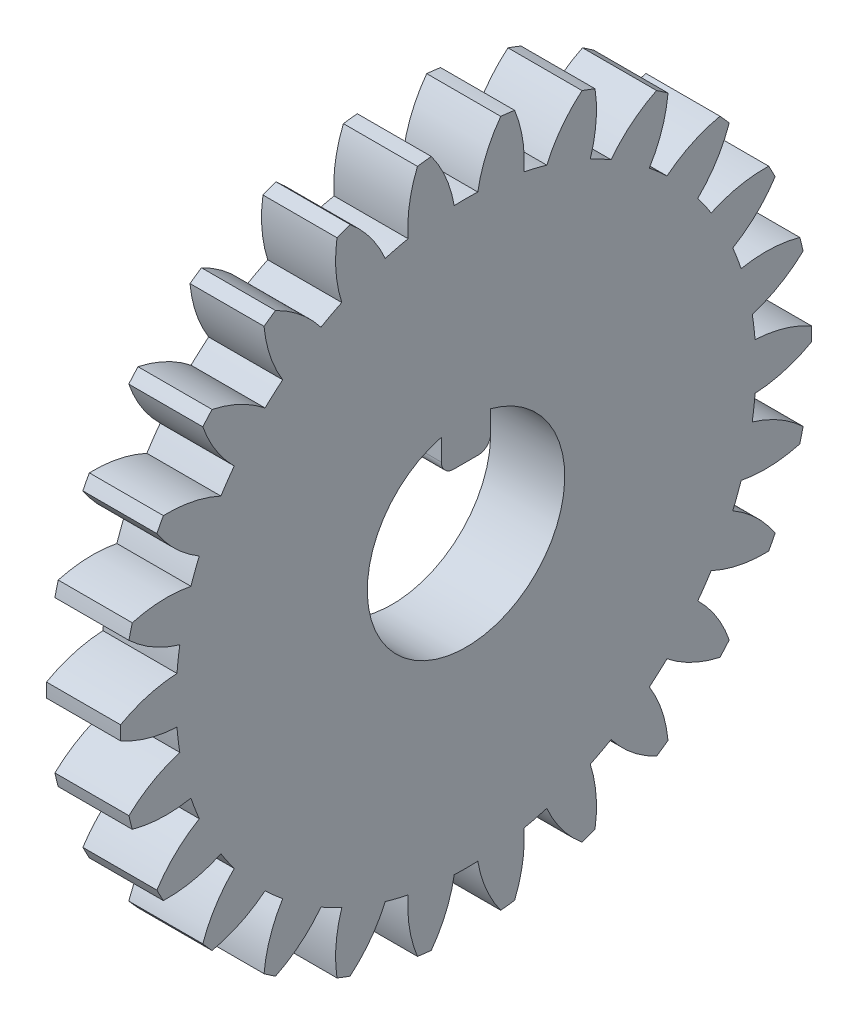
SolidWorks part; units mm, degrees
ref_plane "Plane1" through (0, 0, 0) normal (0, 0, 1) x (1, 0, 0)
ref_plane "Plane2" through (0, 0, 0) normal (0, 1, 0) x (1, 0, 0)
ref_plane "Plane3" through (0, 0, 0) normal (1, 0, 0) x (0, 0, -1)
sketch "HoldingSke" plane through (0, 0, 0) normal (0, 1, 0) x (1, 0, 0)
  line L0 (0, 0) -> (0.8988, -0.4384)
  line L1 (-15, 0) -> (100, 0) construction
  line L2 (0, 0) -> (-2.1039, 2.3779)
  line L3 (0, 0) -> (-11.863, 4.5341)
  line L4 (0, 0) -> (7.762, 3.7858)
  line L5 (0, 0) -> (-46.8476, -17.4728)
  line L6 (0, 0) -> (-2.4869, -1.6779)
  line L7 (-2.1039, 2.3779) -> (8.6586, 51.2059)
  line L8 (-76.2, 54.61) -> (-74.8, 54.61)
  line L9 (-71.009, 38.7566) -> (-53.1078, 45.2721)
  line L10 (-76.2, 71.12) -> (104.1128, 71.12)
  line L11 (0, 0) -> (-3, 0)
  line L12 (-76.2, 101.6) -> (-76.162, 101.6)
  line L13 (24.9733, 27.94) -> (52.9518, 28.4284)
  line L14 (24.9733, 27.94) -> (24.9743, 27.94)
  line L15 (24.9733, 27.94) -> (100.4006, 29.5858)
  line L16 (-63.627, -1) -> (-12.827, -1)
  circle A0 centre (0, 0) radius 4
  circle A1 centre (0, 0) radius 11.749
  circle A2 centre (0, 0) radius 37.5
  circle A3 centre (0, 0) radius 4
  dimension "MHD" = 23.498
  dimension "Hub_dia" = 75
  dimension "Bore" = 8
  dimension "MBD" = 8
  dimension "Num_teeth" = 26
  dimension "Pitch" = 1
  dimension "Overall_len" = 50
  dimension "Show_teeth" = 26
  dimension "Thickness" = 3
  dimension "OAL" = 50.0001
  dimension "T_dim" = 1.4
  dimension "Ap" = 20
  dimension "H" = 19.05
  dimension "Pitch_radius" = 180.3128
  dimension "Width" = 3
  dimension "Backlash" = 0.038
  dimension "Addendum_fac" = 1
  dimension "Dedendum_fac" = 1.25
  dimension "Clearance_fac" = 0.25
  dimension "Dedendum_add" = 0.001
  dimension "Module" = 1
sketch "BasProSke" plane through (0, 0, 0) normal (0, 1, 0) x (1, 0, 0)
  line L0 (-10, 0) -> (60, 0) construction
  line L1 (0, 0) -> (0, 14)
  line L2 (0, 0) -> (3, 0)
  line L3 (3, 0) -> (3, 14)
  line L4 (3, 14) -> (0, 14)
  dimension "Thickness" = 3
  dimension "Diameter" = 28
revolve "Base-Revolve" add sketch "BasProSke" angle 360 about L0
sketch "TooCutSke" plane through (0, 0, 0) normal (1, 0, 0) x (0, 0, -1)
  line L1 (0, 0) -> (0, 107) construction
  line L2 (0, 0) -> (-0.8514, 12.9721) construction
  line L3 (0, 0) -> (-3.1292, 25.771) construction
  line L4 (-0.8514, 12.9721) -> (-1.5646, 12.8855) construction
  arc A0 (0.477, 11.7393) -> (-0.477, 11.7393) centre (0, 0) ccw
  arc A1 (1.4241, 13.9529) -> (-1.4241, 13.9529) centre (0, 0) ccw
  circle A2 centre (0, 0) radius 13 construction
  circle A3 centre (0, 0) radius 12.216 construction
  arc A4 (-0.477, 11.7393) -> (-1.4241, 13.9529) centre (-5.6014, 10.8561) ccw
  arc A5 (1.4241, 13.9529) -> (0.477, 11.7393) centre (5.6014, 10.8561) ccw
  dimension "Root_dia" = 23.498
  dimension "Overcut_dia" = 28.0508
  dimension "Pitch_dia" = 26
  dimension "Base_dia" = 24.432
  dimension "Flank_rad" = 5.2
  dimension "Half_ang" = 6.923
  dimension "Half_CT" = 0.7184
extrude "ToothCut" cut sketch "TooCutSke" along normal through all
fillet "Breaks" [suppressed] radius 0.02
fillet "RootFillets" [suppressed] radius 0.251
pattern_circular "TeethCuts" count 26 every 13.846 about axis through (-10, 0, 0) along (1, 0, 0) of "ToothCut", "RootFillets", "Breaks"
sketch "HubNeaOneSke" plane through (0, 0, 0) normal (-1, 0, 0) x (0, 0, 1)
  circle A0 centre (0, 0) radius 11.749
  dimension "Diameter" = 23.498
extrude "HubNearOne" [suppressed] add sketch "HubNeaOneSke" along normal blind 47.0001
sketch "HubNeaBotSke" plane through (0, 0, 0) normal (-1, 0, 0) x (0, 0, 1)
  circle A0 centre (0, 0) radius 11.749
  dimension "Diameter" = 23.498
extrude "HubNearBoth" [suppressed] add sketch "HubNeaBotSke" along normal blind 23.5
ref_plane "FarPln" through (3, 0, 0) normal (1, 0, 0) x (0, 0, -1)
sketch "HubFarSke" plane through (3, 0, 0) normal (1, 0, 0) x (0, 0, -1)
  circle A0 centre (0, 0) radius 11.749
  dimension "Diameter" = 23.498
extrude "HubFar" [suppressed] add sketch "HubFarSke" along normal blind 23.5
sketch "BorSke" plane through (0, 0, 0) normal (1, 0, 0) x (0, 0, -1)
  circle A0 centre (0, 0) radius 4
  dimension "Diameter" = 8
extrude "Bore" cut sketch "BorSke" along normal mid plane 100.0001
sketch "KeySke" plane through (0, 0, 0) normal (1, 0, 0) x (0, 0, -1)
  line L0 (-1, 0) -> (-1, 5.4)
  line L1 (-1, 5.4) -> (1, 5.4)
  line L2 (1, 5.4) -> (1, 0)
  line L3 (0, 0) -> (0, 34) construction
  line L4 (-1, 0) -> (1, 0)
  dimension "Offset" = 5.4
  dimension "Width" = 2
extrude "Keyway" [suppressed] cut sketch "KeySke" along normal mid plane 100.0001
pattern_circular "Keyway2" [suppressed] count 2 every 90 about axis through (-10, 0, 0) along (1, 0, 0)
sketch "Szkic1" plane through (3, 0, 0) normal (1, 0, 0) x (0, 0, -1)
  line L0 (0, 4) -> (-1, 4)
  line L1 (-1, 4) -> (-1, 3)
  line L2 (-0.5, 2.5) -> (0.5, 2.5)
  line L3 (0, 4) -> (1, 4)
  line L4 (1, 4) -> (1, 3)
  line L5 (0, 4) -> (0, 0) construction
  circle A0 centre (0, 0) radius 4 construction
  arc A1 (0.5, 2.5) -> (1, 3) centre (0.5, 3) ccw
  arc A2 (-1, 3) -> (-0.5, 2.5) centre (-0.5, 3) ccw
  point P11 (1, 2.5)
  point P14 (-1, 2.5)
  dimension "D3" = 0.5
  dimension "D1" = 2
  dimension "D2" = 1.5
extrude "Dodanie-wyciągnięcie1" add sketch "Szkic1" against normal blind 3
equation "' \"Module@HoldingSke\" = 6.35"
equation "' \"Num_teeth@HoldingSke\" = 12"
equation "' \"Ap@HoldingSke\" =  20"
equation "' \"Ap@HoldingSke\" = 20"
equation "' \"Width@HoldingSke\" = 0.5 * 25.4"
equation "' \"Hub_dia@HoldingSke\"= 1 * 25.4"
equation "' \"Hub_dia@HoldingSke\" = 1 * 25.4"
equation "' \"Overall_len@HoldingSke\" = 1.0 * 25.4"
equation "' \"Bore@HoldingSke\" = 0.75 * 25.4"
equation "' \"T_dim@HoldingSke\" = 0.1 * 25.4"
equation "' \"Width@KeySke\" = 0.25 * 25.4"
equation "' \"Show_teeth@HoldingSke\" = 13"
equation "' \"Backlash@HoldingSke\" = 0.009 * 25.4"
equation "' \"Addendum_fac@HoldingSke\" = 1.0"
equation "' \"Dedendum_fac@HoldingSke\" = 1.25"
equation "' \"Dedendum_add@HoldingSke\" = 0.00005 * 25.4"
equation "' \"Clearance_fac@HoldingSke\" = 0.25"
equation "\"Pitch@HoldingSke\" = 1 / \"Module@HoldingSke\""
equation "\"Overcut_dia@TooCutSke\" = (\"Num_teeth@HoldingSke\" + 2 * \"Addendum_fac@HoldingSke\") / \"Pitch@HoldingSke\" + 0.002 * 25.4"
equation "\"Pitch_dia@TooCutSke\" = \"Num_teeth@HoldingSke\" / \"Pitch@HoldingSke\""
equation "\"Base_dia@TooCutSke\" = \"Num_teeth@HoldingSke\" / \"Pitch@HoldingSke\" * cos((\"Ap@HoldingSke\"  * 3.14159265 / 180))"
equation "\"Root_dia@TooCutSke\" = (\"Num_teeth@HoldingSke\" + 2) / \"Pitch@HoldingSke\" - 2 * (\"Addendum_fac@HoldingSke\" + \"Dedendum_fac@HoldingSke\") / \"Pitch@HoldingSke\" - \"Dedendum_add@HoldingSke\" * 2"
equation "\"Half_ang@TooCutSke\" = 180 / \"Num_teeth@HoldingSke\""
equation "\"Half_CT@TooCutSke\" = \"Num_teeth@HoldingSke\" / \"Pitch@HoldingSke\" * sin((3.14159265 / 2 / \"Num_teeth@HoldingSke\")) / 2 - 7 * \"Backlash@HoldingSke\" / 4"
equation "\"Flank_rad@TooCutSke\" = \"Num_teeth@HoldingSke\" / \"Pitch@HoldingSke\" / 5"
equation "\"Radius@RootFillets\" = \"Clearance_fac@HoldingSke\" / \"Pitch@HoldingSke\" + \"Dedendum_add@HoldingSke\""
equation "\"Break_rad@Breaks\" = 0.02 / \"Pitch@HoldingSke\""
equation "\"Thickness@HoldingSke\" = \"Width@HoldingSke\""
equation "\"OAL@HoldingSke\" = \"Thickness@HoldingSke\""
equation "\"MHD@HoldingSke\" = (\"Num_teeth@HoldingSke\" + 2) / \"Pitch@HoldingSke\" - 2 * (\"Addendum_fac@HoldingSke\" + \"Dedendum_fac@HoldingSke\")  / \"Pitch@HoldingSke\" - \"Dedendum_add@HoldingSke\" * 2"
equation "\"MBD@HoldingSke\" = (\"Num_teeth@HoldingSke\" + 2) / \"Pitch@HoldingSke\" - 2 * (\"Addendum_fac@HoldingSke\" + \"Dedendum_fac@HoldingSke\")  / \"Pitch@HoldingSke\" - \"Dedendum_add@HoldingSke\" * 2 - 0.002 * 25.4"
equation "\"MHD@HoldingSke\" = ((sgn( \"MHD@HoldingSke\" - \"Hub_dia@HoldingSke\" )-1)*( \"MHD@HoldingSke\" - \"Hub_dia@HoldingSke\" ))/-2+ \"Hub_dia@HoldingSke\""
equation "\"MBD@HoldingSke\" = ((sgn( \"MBD@HoldingSke\" - \"Bore@HoldingSke\" )-1)*( \"MBD@HoldingSke\" - \"Bore@HoldingSke\" ))/-2+ \"Bore@HoldingSke\""
equation "\"OAL@HoldingSke\" = ((sgn( \"OAL@HoldingSke\" - \"Overall_len@HoldingSke\" )+1)*( \"OAL@HoldingSke\" - \"Overall_len@HoldingSke\" ))/2 + \"Overall_len@HoldingSke\" + 0.000002 * 25.4"
equation "\"Num_teeth@TeethCuts\" = int( \"Show_teeth@HoldingSke\" ) + 1"
equation "\"Num_teeth@TeethCuts\" = ((sgn( \"Num_teeth@TeethCuts\" - \"Num_teeth@HoldingSke\" )-1)*( \"Num_teeth@TeethCuts\" - \"Num_teeth@HoldingSke\" ))/-2+ \"Num_teeth@HoldingSke\""
equation "\"Num_teeth@TeethCuts\" = ((sgn( \"Num_teeth@TeethCuts\" - 2.0)+1)*( \"Num_teeth@TeethCuts\" - 2.0))/2 +2.0"
equation "\"Angle@TeethCuts\" = 360.0 / \"Num_teeth@HoldingSke\""
equation "\"Diameter@BasProSke\" = (\"Num_teeth@HoldingSke\" + 2 * \"Addendum_fac@HoldingSke\") / \"Pitch@HoldingSke\""
equation "\"Thickness@BasProSke\"  = \"Thickness@HoldingSke\""
equation "' \"Fillet_rad@BasProSke\" =  \"Thickness@HoldingSke\" * 0.05"
equation "' \"Fillet_rad@BasProSke\" = \"Thickness@HoldingSke\" * 0.05"
equation "\"MHD@HoldingSke\" = ((sgn( \"MHD@HoldingSke\" - \"Root_dia@TooCutSke\" )-1)*( \"MHD@HoldingSke\" - \"Root_dia@TooCutSke\" ))/-2+ \"Root_dia@TooCutSke\""
equation "\"Diameter@HubNeaOneSke\" = \"MHD@HoldingSke\""
equation "\"Length@HubNearOne\" = \"OAL@HoldingSke\" - \"Thickness@BasProSke\""
equation "\"Diameter@HubNeaBotSke\" = \"MHD@HoldingSke\""
equation "\"Length@HubNearBoth\" = ( \"OAL@HoldingSke\" - \"Thickness@BasProSke\" ) / 2.0"
equation "\"Thickness@FarPln\" = \"Thickness@BasProSke\""
equation "\"Diameter@HubFarSke\" = \"MHD@HoldingSke\""
equation "\"Length@HubFar\" = ( \"OAL@HoldingSke\" - \"Thickness@BasProSke\" ) / 2.0"
equation "\"Diameter@BorSke\" = \"MBD@HoldingSke\""
equation "\"D1@Bore\" = \"OAL@HoldingSke\" * 2.0"
equation "\"D1@Keyway\" = \"OAL@HoldingSke\" * 2.0"
equation "\"Offset@KeySke\" = \"T_dim@HoldingSke\" + \"MBD@HoldingSke\" / 2.0"
